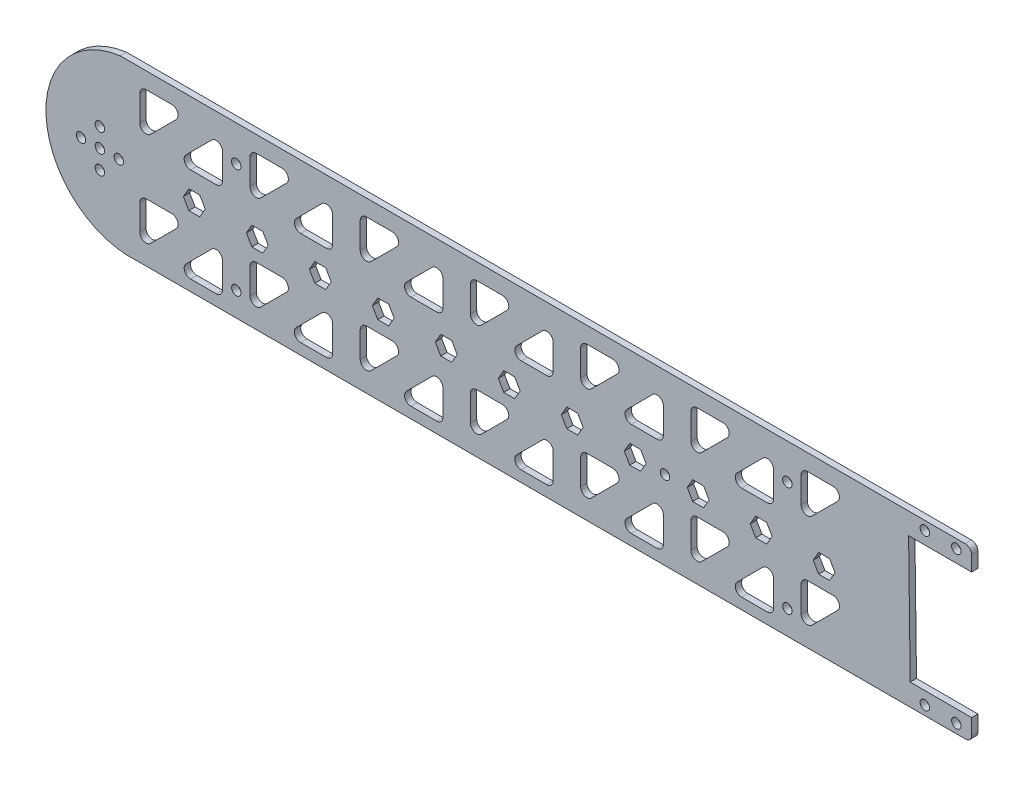
SolidWorks part; units mm, degrees
ref_plane "Ön Düzlem" through (0, 0, 0) normal (0, 0, 1) x (1, 0, 0)
ref_plane "Üst Düzlem" through (0, 0, 0) normal (0, 1, 0) x (1, 0, 0)
ref_plane "Sağ Düzlem" through (0, 0, 0) normal (1, 0, 0) x (0, 0, -1)
sketch "Çizim1" plane through (0, 0, 0) normal (0, 0, 1) x (1, 0, 0)
  line L0 (0, 34.9435) -> (0, -25.0192) construction
  line L1 (-123.6821, 28.6804) -> (123.6821, 28.6804)
  line L3 (-118.1627, -25.0192) -> (118.1627, -25.0192)
  line L5 (-150.2336, 30.0467) -> (150, -30) construction
  line L6 (123.6821, 28.6804) -> (137.2391, 28.6804)
  line L7 (-0.1168, 0.0234) -> (-130.1063, 0.0234) construction
  line L8 (-130.1063, 6.0234) -> (-130.1063, -6.1534) construction
  line L9 (-18.3887, -2.9789) -> (-16.6527, 0.0189)
  line L10 (1.6113, -2.9789) -> (3.3473, 0.0189)
  line L11 (3.3473, 0.0189) -> (1.6191, 3.0211)
  line L12 (1.6191, 3.0211) -> (-1.845, 3.0256)
  line L13 (-1.845, 3.0256) -> (-3.5809, 0.0279)
  line L14 (-3.5809, 0.0279) -> (-1.8528, -2.9744)
  line L15 (-1.8528, -2.9744) -> (1.6113, -2.9789)
  line L16 (-16.6527, 0.0189) -> (-18.3809, 3.0211)
  line L17 (-18.3809, 3.0211) -> (-21.845, 3.0256)
  line L18 (-21.845, 3.0256) -> (-23.5809, 0.0279)
  line L19 (-23.5809, 0.0279) -> (-21.8528, -2.9744)
  line L20 (-21.8528, -2.9744) -> (-18.3887, -2.9789)
  line L21 (-38.3887, -2.9789) -> (-36.6527, 0.0189)
  line L22 (-36.6527, 0.0189) -> (-38.3809, 3.0211)
  line L23 (-38.3809, 3.0211) -> (-41.845, 3.0256)
  line L24 (-41.845, 3.0256) -> (-43.5809, 0.0279)
  line L25 (-43.5809, 0.0279) -> (-41.8528, -2.9744)
  line L26 (-41.8528, -2.9744) -> (-38.3887, -2.9789)
  line L27 (-58.3887, -2.9789) -> (-56.6527, 0.0189)
  line L28 (-56.6527, 0.0189) -> (-58.3809, 3.0211)
  line L29 (-58.3809, 3.0211) -> (-61.845, 3.0256)
  line L30 (-61.845, 3.0256) -> (-63.5809, 0.0279)
  line L31 (-63.5809, 0.0279) -> (-61.8528, -2.9744)
  line L32 (-61.8528, -2.9744) -> (-58.3887, -2.9789)
  line L33 (-78.3887, -2.9789) -> (-76.6527, 0.0189)
  line L34 (-76.6527, 0.0189) -> (-78.3809, 3.0211)
  line L35 (-78.3809, 3.0211) -> (-81.845, 3.0256)
  line L36 (-81.845, 3.0256) -> (-83.5809, 0.0279)
  line L37 (-83.5809, 0.0279) -> (-81.8528, -2.9744)
  line L38 (-81.8528, -2.9744) -> (-78.3887, -2.9789)
  line L39 (-98.3887, -2.9789) -> (-96.6527, 0.0189)
  line L40 (-96.6527, 0.0189) -> (-98.3809, 3.0211)
  line L41 (-98.3809, 3.0211) -> (-101.845, 3.0256)
  line L42 (-101.845, 3.0256) -> (-103.5809, 0.0279)
  line L43 (-103.5809, 0.0279) -> (-101.8528, -2.9744)
  line L44 (-101.8528, -2.9744) -> (-98.3887, -2.9789)
  line L45 (21.6113, -2.9789) -> (23.3473, 0.0189)
  line L46 (18.1472, -2.9744) -> (21.6113, -2.9789)
  line L47 (16.4191, 0.0279) -> (18.1472, -2.9744)
  line L48 (18.155, 3.0256) -> (16.4191, 0.0279)
  line L49 (21.6191, 3.0211) -> (18.155, 3.0256)
  line L50 (23.3473, 0.0189) -> (21.6191, 3.0211)
  line L51 (41.6113, -2.9789) -> (43.3473, 0.0189)
  line L52 (38.1472, -2.9744) -> (41.6113, -2.9789)
  line L53 (36.4191, 0.0279) -> (38.1472, -2.9744)
  line L54 (38.155, 3.0256) -> (36.4191, 0.0279)
  line L55 (41.6191, 3.0211) -> (38.155, 3.0256)
  line L56 (43.3473, 0.0189) -> (41.6191, 3.0211)
  line L57 (61.6113, -2.9789) -> (63.3473, 0.0189)
  line L58 (58.1472, -2.9744) -> (61.6113, -2.9789)
  line L59 (56.4191, 0.0279) -> (58.1472, -2.9744)
  line L60 (58.155, 3.0256) -> (56.4191, 0.0279)
  line L61 (61.6191, 3.0211) -> (58.155, 3.0256)
  line L62 (63.3473, 0.0189) -> (61.6191, 3.0211)
  line L63 (81.6113, -2.9789) -> (83.3473, 0.0189)
  line L64 (78.1472, -2.9744) -> (81.6113, -2.9789)
  line L65 (76.4191, 0.0279) -> (78.1472, -2.9744)
  line L66 (78.155, 3.0256) -> (76.4191, 0.0279)
  line L67 (81.6191, 3.0211) -> (78.155, 3.0256)
  line L68 (83.3473, 0.0189) -> (81.6191, 3.0211)
  line L69 (101.6113, -2.9789) -> (103.3473, 0.0189)
  line L70 (98.1472, -2.9744) -> (101.6113, -2.9789)
  line L71 (96.4191, 0.0279) -> (98.1472, -2.9744)
  line L72 (98.155, 3.0256) -> (96.4191, 0.0279)
  line L73 (101.6191, 3.0211) -> (98.155, 3.0256)
  line L74 (103.3473, 0.0189) -> (101.6191, 3.0211)
  line L75 (-117.433, 15.462) -> (117.433, 15.462) construction
  line L76 (-117.433, 21.4866) -> (-117.433, 13.315)
  line L77 (-115.433, 23.4866) -> (-107.2614, 23.4866)
  line L78 (-105.8472, 20.0724) -> (-114.0187, 11.9008)
  line L79 (-94.5849, 20.0724) -> (-102.7565, 11.9008)
  line L80 (-101.3423, 8.4866) -> (-93.1707, 8.4866)
  line L81 (-91.1707, 10.4866) -> (-91.1707, 18.6582)
  line L82 (-82.433, 21.4866) -> (-82.433, 13.315)
  line L83 (-80.433, 23.4866) -> (-72.2614, 23.4866)
  line L84 (-70.8472, 20.0724) -> (-79.0187, 11.9008)
  line L85 (-59.5849, 20.0724) -> (-67.7565, 11.9008)
  line L86 (-66.3423, 8.4866) -> (-58.1707, 8.4866)
  line L87 (-56.1707, 10.4866) -> (-56.1707, 18.6582)
  line L88 (-47.433, 21.4866) -> (-47.433, 13.315)
  line L89 (-45.433, 23.4866) -> (-37.2614, 23.4866)
  line L90 (-35.8472, 20.0724) -> (-44.0187, 11.9008)
  line L91 (-24.5849, 20.0724) -> (-32.7565, 11.9008)
  line L92 (-31.3423, 8.4866) -> (-23.1707, 8.4866)
  line L93 (-21.1707, 10.4866) -> (-21.1707, 18.6582)
  line L94 (-12.433, 21.4866) -> (-12.433, 13.315)
  line L95 (-10.433, 23.4866) -> (-2.2614, 23.4866)
  line L96 (-0.8472, 20.0724) -> (-9.0187, 11.9008)
  line L97 (10.4151, 20.0724) -> (2.2435, 11.9008)
  line L98 (3.6577, 8.4866) -> (11.8293, 8.4866)
  line L99 (13.8293, 10.4866) -> (13.8293, 18.6582)
  line L100 (22.567, 21.4866) -> (22.567, 13.315)
  line L101 (24.567, 23.4866) -> (32.7386, 23.4866)
  line L102 (34.1528, 20.0724) -> (25.9813, 11.9008)
  line L103 (45.4151, 20.0724) -> (37.2435, 11.9008)
  line L104 (38.6577, 8.4866) -> (46.8293, 8.4866)
  line L105 (48.8293, 10.4866) -> (48.8293, 18.6582)
  line L106 (57.567, 21.4866) -> (57.567, 13.315)
  line L107 (59.567, 23.4866) -> (67.7386, 23.4866)
  line L108 (69.1528, 20.0724) -> (60.9813, 11.9008)
  line L109 (80.4151, 20.0724) -> (72.2435, 11.9008)
  line L110 (73.6577, 8.4866) -> (81.8293, 8.4866)
  line L111 (83.8293, 10.4866) -> (83.8293, 18.6582)
  line L112 (92.567, 21.4866) -> (92.567, 13.315)
  line L113 (94.567, 23.4866) -> (102.7386, 23.4866)
  line L114 (104.1528, 20.0724) -> (95.9813, 11.9008)
  line L118 (-82.433, -8.5134) -> (-82.433, -16.685)
  line L119 (-80.433, -6.5134) -> (-72.2614, -6.5134)
  line L120 (-70.8472, -9.9276) -> (-79.0187, -18.0992)
  line L121 (-59.5849, -9.9276) -> (-67.7565, -18.0992)
  line L122 (-66.3423, -21.5134) -> (-58.1707, -21.5134)
  line L123 (-56.1707, -19.5134) -> (-56.1707, -11.3418)
  line L124 (-47.433, -8.5134) -> (-47.433, -16.685)
  line L125 (-45.433, -6.5134) -> (-37.2614, -6.5134)
  line L126 (-35.8472, -9.9276) -> (-44.0187, -18.0992)
  line L127 (-24.5849, -9.9276) -> (-32.7565, -18.0992)
  line L128 (-31.3423, -21.5134) -> (-23.1707, -21.5134)
  line L129 (-21.1707, -19.5134) -> (-21.1707, -11.3418)
  line L130 (-12.433, -8.5134) -> (-12.433, -16.685)
  line L131 (-10.433, -6.5134) -> (-2.2614, -6.5134)
  line L132 (-0.8472, -9.9276) -> (-9.0187, -18.0992)
  line L133 (10.4151, -9.9276) -> (2.2435, -18.0992)
  line L134 (3.6577, -21.5134) -> (11.8293, -21.5134)
  line L135 (13.8293, -19.5134) -> (13.8293, -11.3418)
  line L136 (22.567, -8.5134) -> (22.567, -16.685)
  line L137 (24.567, -6.5134) -> (32.7386, -6.5134)
  line L138 (34.1528, -9.9276) -> (25.9813, -18.0992)
  line L139 (45.4151, -9.9276) -> (37.2435, -18.0992)
  line L140 (38.6577, -21.5134) -> (46.8293, -21.5134)
  line L141 (48.8293, -19.5134) -> (48.8293, -11.3418)
  line L142 (57.567, -8.5134) -> (57.567, -16.685)
  line L143 (59.567, -6.5134) -> (67.7386, -6.5134)
  line L144 (69.1528, -9.9276) -> (60.9813, -18.0992)
  line L145 (80.4151, -9.9276) -> (72.2435, -18.0992)
  line L146 (73.6577, -21.5134) -> (81.8293, -21.5134)
  line L147 (83.8293, -19.5134) -> (83.8293, -11.3418)
  line L148 (92.567, -8.5134) -> (92.567, -16.685)
  line L149 (94.567, -6.5134) -> (102.7386, -6.5134)
  line L150 (104.1528, -9.9276) -> (95.9813, -18.0992)
  line L154 (-117.433, -8.5134) -> (-117.433, -16.685)
  line L155 (-115.433, -6.5134) -> (-107.2614, -6.5134)
  line L156 (-105.8472, -9.9276) -> (-114.0187, -18.0992)
  line L157 (-94.5849, -9.9276) -> (-102.7565, -18.0992)
  line L158 (-101.3423, -21.5134) -> (-93.1707, -21.5134)
  line L159 (-91.1707, -19.5134) -> (-91.1707, -11.3418)
  line L160 (-0.1168, 0.0234) -> (126.9645, 1.6425) construction
  line L168 (108.6577, 8.4866) -> (116.8293, 8.4866) [skipped]
  line L169 (118.8293, 10.4866) -> (118.8293, 18.6582) [skipped]
  line L170 (118.8293, -19.5134) -> (118.8293, -11.3418) [skipped]
  line L171 (115.4151, -9.9276) -> (107.2435, -18.0992) [skipped]
  line L172 (108.6577, -21.5134) -> (116.8293, -21.5134) [skipped]
  line L173 (115.4151, 20.0724) -> (110.8046, 15.462) [skipped]
  line L176 (110.2391, 21.9008) -> (130.2391, -18.0992) construction
  line L177 (110.2391, -18.0992) -> (130.2391, 21.9008) construction
  line L178 (137.2391, -25.0192) -> (118.1627, -25.0192)
  line L179 (146.7064, 21.9008) -> (126.7064, 21.9008)
  line L180 (146.7468, -18.1182) -> (127.2163, -18.1182)
  line L181 (126.7064, 21.9008) -> (127.2226, -18.6158)
  line L182 (137.2391, 28.6804) -> (144.7064, 28.6804)
  line L183 (146.7064, 26.6804) -> (146.7064, 21.9008)
  line L184 (146.7468, -18.1182) -> (146.7468, -23.0192)
  line L185 (144.7468, -25.0192) -> (137.2391, -25.0192)
  arc A0 (-123.6821, 28.6804) -> (-118.1627, -25.0192) centre (-120.2391, 1.9008) ccw
  arc A1 (124.105, -24.821) -> (118.1627, -25.0192) centre (120.2391, 1.9008) cw
  circle A2 centre (-130.1063, 0.0234) radius 10
  circle A3 centre (-130.1063, 6.0234) radius 1.5
  circle A4 centre (-130.1063, -5.9766) radius 1.5
  circle A5 centre (-136.1063, 0.0234) radius 1.5
  circle A6 centre (-130.1063, 6.0234) radius 1.5
  circle A7 centre (-124.1063, 0.0234) radius 1.5
  circle A8 centre (-130.1063, 0.0234) radius 1.5
  circle A15 centre (-0.1168, 0.0234) radius 3 construction
  arc A16 (-101.3423, 8.4866) -> (-102.7565, 11.9008) centre (-101.3423, 10.4866) cw
  arc A17 (-93.1707, 8.4866) -> (-91.1707, 10.4866) centre (-93.1707, 10.4866) ccw
  arc A18 (-91.1707, 18.6582) -> (-94.5849, 20.0724) centre (-93.1707, 18.6582) ccw
  arc A19 (-114.0187, 11.9008) -> (-117.433, 13.315) centre (-115.433, 13.315) cw
  arc A20 (-107.2614, 23.4866) -> (-105.8472, 20.0724) centre (-107.2614, 21.4866) cw
  arc A21 (-117.433, 21.4866) -> (-115.433, 23.4866) centre (-115.433, 21.4866) cw
  arc A22 (-72.2614, 23.4866) -> (-70.8472, 20.0724) centre (-72.2614, 21.4866) cw
  arc A23 (-82.433, 21.4866) -> (-80.433, 23.4866) centre (-80.433, 21.4866) cw
  arc A24 (-79.0187, 11.9008) -> (-82.433, 13.315) centre (-80.433, 13.315) cw
  arc A25 (-66.3423, 8.4866) -> (-67.7565, 11.9008) centre (-66.3423, 10.4866) cw
  arc A26 (-58.1707, 8.4866) -> (-56.1707, 10.4866) centre (-58.1707, 10.4866) ccw
  arc A27 (-56.1707, 18.6582) -> (-59.5849, 20.0724) centre (-58.1707, 18.6582) ccw
  arc A28 (-37.2614, 23.4866) -> (-35.8472, 20.0724) centre (-37.2614, 21.4866) cw
  arc A29 (-47.433, 21.4866) -> (-45.433, 23.4866) centre (-45.433, 21.4866) cw
  arc A30 (-44.0187, 11.9008) -> (-47.433, 13.315) centre (-45.433, 13.315) cw
  arc A31 (-31.3423, 8.4866) -> (-32.7565, 11.9008) centre (-31.3423, 10.4866) cw
  arc A32 (-23.1707, 8.4866) -> (-21.1707, 10.4866) centre (-23.1707, 10.4866) ccw
  arc A33 (-21.1707, 18.6582) -> (-24.5849, 20.0724) centre (-23.1707, 18.6582) ccw
  arc A34 (-2.2614, 23.4866) -> (-0.8472, 20.0724) centre (-2.2614, 21.4866) cw
  arc A35 (-12.433, 21.4866) -> (-10.433, 23.4866) centre (-10.433, 21.4866) cw
  arc A36 (-9.0187, 11.9008) -> (-12.433, 13.315) centre (-10.433, 13.315) cw
  arc A37 (3.6577, 8.4866) -> (2.2435, 11.9008) centre (3.6577, 10.4866) cw
  arc A38 (11.8293, 8.4866) -> (13.8293, 10.4866) centre (11.8293, 10.4866) ccw
  arc A39 (13.8293, 18.6582) -> (10.4151, 20.0724) centre (11.8293, 18.6582) ccw
  arc A40 (32.7386, 23.4866) -> (34.1528, 20.0724) centre (32.7386, 21.4866) cw
  arc A41 (22.567, 21.4866) -> (24.567, 23.4866) centre (24.567, 21.4866) cw
  arc A42 (25.9813, 11.9008) -> (22.567, 13.315) centre (24.567, 13.315) cw
  arc A43 (38.6577, 8.4866) -> (37.2435, 11.9008) centre (38.6577, 10.4866) cw
  arc A44 (46.8293, 8.4866) -> (48.8293, 10.4866) centre (46.8293, 10.4866) ccw
  arc A45 (48.8293, 18.6582) -> (45.4151, 20.0724) centre (46.8293, 18.6582) ccw
  arc A46 (67.7386, 23.4866) -> (69.1528, 20.0724) centre (67.7386, 21.4866) cw
  arc A47 (57.567, 21.4866) -> (59.567, 23.4866) centre (59.567, 21.4866) cw
  arc A48 (60.9813, 11.9008) -> (57.567, 13.315) centre (59.567, 13.315) cw
  arc A49 (73.6577, 8.4866) -> (72.2435, 11.9008) centre (73.6577, 10.4866) cw
  arc A50 (81.8293, 8.4866) -> (83.8293, 10.4866) centre (81.8293, 10.4866) ccw
  arc A51 (83.8293, 18.6582) -> (80.4151, 20.0724) centre (81.8293, 18.6582) ccw
  arc A52 (102.7386, 23.4866) -> (104.1528, 20.0724) centre (102.7386, 21.4866) cw
  arc A53 (92.567, 21.4866) -> (94.567, 23.4866) centre (94.567, 21.4866) cw
  arc A54 (95.9813, 11.9008) -> (92.567, 13.315) centre (94.567, 13.315) cw
  arc A58 (-72.2614, -6.5134) -> (-70.8472, -9.9276) centre (-72.2614, -8.5134) cw
  arc A59 (-82.433, -8.5134) -> (-80.433, -6.5134) centre (-80.433, -8.5134) cw
  arc A60 (-79.0187, -18.0992) -> (-82.433, -16.685) centre (-80.433, -16.685) cw
  arc A61 (-66.3423, -21.5134) -> (-67.7565, -18.0992) centre (-66.3423, -19.5134) cw
  arc A62 (-58.1707, -21.5134) -> (-56.1707, -19.5134) centre (-58.1707, -19.5134) ccw
  arc A63 (-56.1707, -11.3418) -> (-59.5849, -9.9276) centre (-58.1707, -11.3418) ccw
  arc A64 (-37.2614, -6.5134) -> (-35.8472, -9.9276) centre (-37.2614, -8.5134) cw
  arc A65 (-47.433, -8.5134) -> (-45.433, -6.5134) centre (-45.433, -8.5134) cw
  arc A66 (-44.0187, -18.0992) -> (-47.433, -16.685) centre (-45.433, -16.685) cw
  arc A67 (-31.3423, -21.5134) -> (-32.7565, -18.0992) centre (-31.3423, -19.5134) cw
  arc A68 (-23.1707, -21.5134) -> (-21.1707, -19.5134) centre (-23.1707, -19.5134) ccw
  arc A69 (-21.1707, -11.3418) -> (-24.5849, -9.9276) centre (-23.1707, -11.3418) ccw
  arc A70 (-2.2614, -6.5134) -> (-0.8472, -9.9276) centre (-2.2614, -8.5134) cw
  arc A71 (-12.433, -8.5134) -> (-10.433, -6.5134) centre (-10.433, -8.5134) cw
  arc A72 (-9.0187, -18.0992) -> (-12.433, -16.685) centre (-10.433, -16.685) cw
  arc A73 (3.6577, -21.5134) -> (2.2435, -18.0992) centre (3.6577, -19.5134) cw
  arc A74 (11.8293, -21.5134) -> (13.8293, -19.5134) centre (11.8293, -19.5134) ccw
  arc A75 (13.8293, -11.3418) -> (10.4151, -9.9276) centre (11.8293, -11.3418) ccw
  arc A76 (32.7386, -6.5134) -> (34.1528, -9.9276) centre (32.7386, -8.5134) cw
  arc A77 (22.567, -8.5134) -> (24.567, -6.5134) centre (24.567, -8.5134) cw
  arc A78 (25.9813, -18.0992) -> (22.567, -16.685) centre (24.567, -16.685) cw
  arc A79 (38.6577, -21.5134) -> (37.2435, -18.0992) centre (38.6577, -19.5134) cw
  arc A80 (46.8293, -21.5134) -> (48.8293, -19.5134) centre (46.8293, -19.5134) ccw
  arc A81 (48.8293, -11.3418) -> (45.4151, -9.9276) centre (46.8293, -11.3418) ccw
  arc A82 (67.7386, -6.5134) -> (69.1528, -9.9276) centre (67.7386, -8.5134) cw
  arc A83 (57.567, -8.5134) -> (59.567, -6.5134) centre (59.567, -8.5134) cw
  arc A84 (60.9813, -18.0992) -> (57.567, -16.685) centre (59.567, -16.685) cw
  arc A85 (73.6577, -21.5134) -> (72.2435, -18.0992) centre (73.6577, -19.5134) cw
  arc A86 (81.8293, -21.5134) -> (83.8293, -19.5134) centre (81.8293, -19.5134) ccw
  arc A87 (83.8293, -11.3418) -> (80.4151, -9.9276) centre (81.8293, -11.3418) ccw
  arc A88 (102.7386, -6.5134) -> (104.1528, -9.9276) centre (102.7386, -8.5134) cw
  arc A89 (92.567, -8.5134) -> (94.567, -6.5134) centre (94.567, -8.5134) cw
  arc A90 (95.9813, -18.0992) -> (92.567, -16.685) centre (94.567, -16.685) cw
  arc A94 (-107.2614, -6.5134) -> (-105.8472, -9.9276) centre (-107.2614, -8.5134) cw
  arc A95 (-117.433, -8.5134) -> (-115.433, -6.5134) centre (-115.433, -8.5134) cw
  arc A96 (-114.0187, -18.0992) -> (-117.433, -16.685) centre (-115.433, -16.685) cw
  arc A97 (-101.3423, -21.5134) -> (-102.7565, -18.0992) centre (-101.3423, -19.5134) cw
  arc A98 (-93.1707, -21.5134) -> (-91.1707, -19.5134) centre (-93.1707, -19.5134) ccw
  arc A99 (-91.1707, -11.3418) -> (-94.5849, -9.9276) centre (-93.1707, -11.3418) ccw
  arc A100 (116.8293, 8.4866) -> (118.8293, 10.4866) centre (116.8293, 10.4866) ccw [skipped]
  arc A101 (108.6577, 8.4866) -> (107.2435, 11.9008) centre (108.6577, 10.4866) cw [skipped]
  arc A102 (118.8293, -11.3418) -> (115.4151, -9.9276) centre (116.8293, -11.3418) ccw [skipped]
  arc A103 (108.6577, -21.5134) -> (107.2435, -18.0992) centre (108.6577, -19.5134) cw [skipped]
  arc A104 (118.8293, 18.6582) -> (115.4151, 20.0724) centre (116.8293, 18.6582) ccw [skipped]
  arc A105 (116.8293, -21.5134) -> (118.8293, -19.5134) centre (116.8293, -19.5134) ccw [skipped]
  arc A108 (144.7468, -25.0192) -> (146.7468, -23.0192) centre (144.7468, -23.0192) ccw
  arc A109 (144.7064, 28.6804) -> (146.7064, 26.6804) centre (144.7064, 26.6804) cw
  circle A110 centre (131.8598, 25.9008) radius 1.5
  circle A111 centre (141.8598, 25.9008) radius 1.5
  circle A112 centre (131.8598, -22.0992) radius 1.5
  circle A113 centre (141.8598, -22.0992) radius 1.5
  point P0 (0, 0)
  point P23 (120.3522, -2.2451)
  point P31 (-130.1063, 0.0234)
  point P124 (-117.433, 8.4866)
  point P127 (-102.433, 23.4866)
  point P130 (-117.433, 23.4866)
  dimension "D1" = 20
  dimension "D3" = 3
  dimension "D6" = 6
  dimension "D10" = 2
  dimension "D16" = 2
  dimension "D4" = 6
  dimension "D8" = 15
  dimension "D9" = 15
  dimension "D13" = 40
  dimension "D14" = 20
  dimension "D15" = 20
  dimension "D7" = 6
  dimension "D11" = 7
  dimension "D12" = 2
  dimension "D5" = 4
extrude "Yükseklik-Ekstrüzyon2" add sketch "Çizim1" along normal blind 2
sketch "Çizim9" plane through (0, 0, 0) normal (0, 0, -1) x (-1, 0, 0)
  line L0 (-92.567, 17.4008) -> (-83.8293, 17.4008) construction
  line L1 (-92.567, 21.4866) -> (-92.567, 13.315) construction
  line L2 (-83.8293, 10.4866) -> (-83.8293, 18.6582) construction
  line L3 (-88.1982, 17.4008) -> (-88.1982, -25.6798) construction
  line L4 (-96.4191, 0.0279) -> (-83.3473, 0.0189) construction
  line L5 (-1.8099, 9.7212) -> (-1.8099, -20.2788) construction
  line L6 (-96.4191, 0.0279) -> (96.6527, 0.0189) construction
  circle A0 centre (-88.1982, 17.4008) radius 1.5
  circle A1 centre (-88.2222, -17.3564) radius 1.5
  arc A2 (-3.6577, 8.4866) -> (-2.2435, 11.9008) centre (-3.6577, 10.4866) ccw construction
  arc A3 (-3.6577, -21.5134) -> (-2.2435, -18.0992) centre (-3.6577, -19.5134) ccw construction
  circle A4 centre (86.8018, 17.4008) radius 1.5
  circle A5 centre (86.7778, -17.3564) radius 1.5
  dimension "D1" = 2
extrude "Kes-Ekstrüzyon5" cut sketch "Çizim9" against normal blind 10
sketch "Çizim10" plane through (0, 0, 2) normal (0, 0, 1) x (1, 0, 0)
  circle A0 centre (49.3473, 0) radius 1.5
  dimension "D1" = 3
  dimension "D2" = 6
extrude "Kes-Ekstrüzyon7" cut sketch "Çizim10" against normal blind 10
